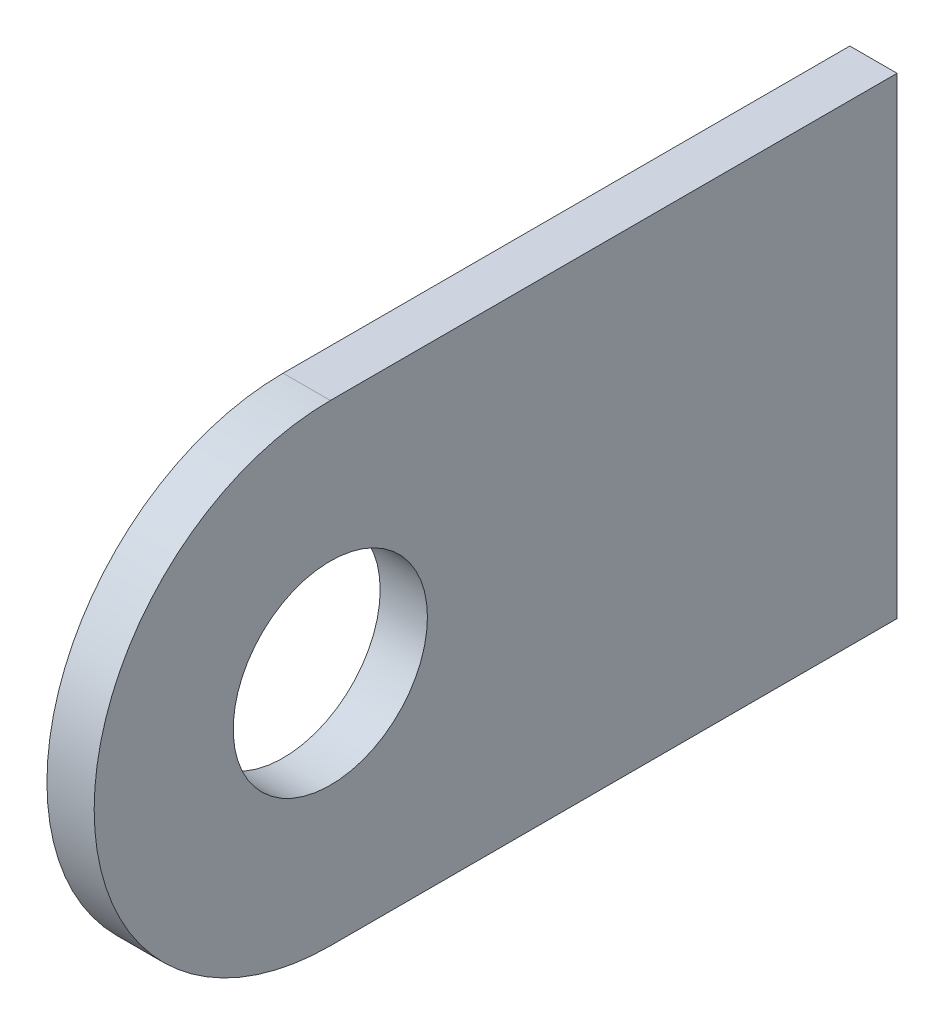
SolidWorks part; units mm, degrees
material "AISI 4130 Steel, annealed at 865C"
ref_plane "X-Y Datum" through (0, 0, 0) normal (0, 0, 1) x (1, 0, 0)
ref_plane "X-Z Datum" through (0, 0, 0) normal (0, 1, 0) x (1, 0, 0)
ref_plane "Y-Z Datum" through (0, 0, 0) normal (1, 0, 0) x (0, 0, -1)
sketch "Sketch1" plane through (0, 0, 0) normal (1, 0, 0) x (0, 0, -1)
  line L0 (3.175, -7.9375) -> (3.175, 7.9375)
  line L4 (-15.875, -7.9375) -> (3.175, -7.9375)
  line L5 (-15.875, 7.9375) -> (3.175, 7.9375)
  arc A1 (-15.875, -7.9375) -> (-15.875, 7.9375) centre (-15.875, 0) cw
  point P3 (0, 0)
  point P4 (3.175, 0)
  point P5 (0, 0)
  point P10 (0, 0)
  dimension "D1" = 19.05
  dimension "D2" = 7.9375
  dimension "D3" = 3.175
extrude "Boss-Extrude1" add sketch "Sketch1" along normal blind 1.5875
hole_wizard "1/4 Clearance Hole1" positions "Sketch2" profile "Sketch3" hole size "1/4" standard "ANSI Inch" end condition through all
sketch "Sketch2" plane through (1.5875, 0, 0) normal (1, 0, 0) x (0, 0, -1)
  point P0 (-15.875, 0)
sketch "Sketch3" plane through (1.5875, 0, 15.875) normal (0, 1, 0) x (0, 0, -1)
  line L0 (0, 0) -> (0, 1.5875)
  line L1 (0, 1.5875) -> (3.2639, 1.5875)
  line L2 (3.2639, 1.5875) -> (3.2639, 0)
  line L5 (3.2639, 0) -> (0, 0)
  line L11 (0, -6.35) -> (0, 107.95) construction
  dimension "Thru Hole Dia." = 6.5278
  dimension "Thru Hole Depth" = 1.5875
